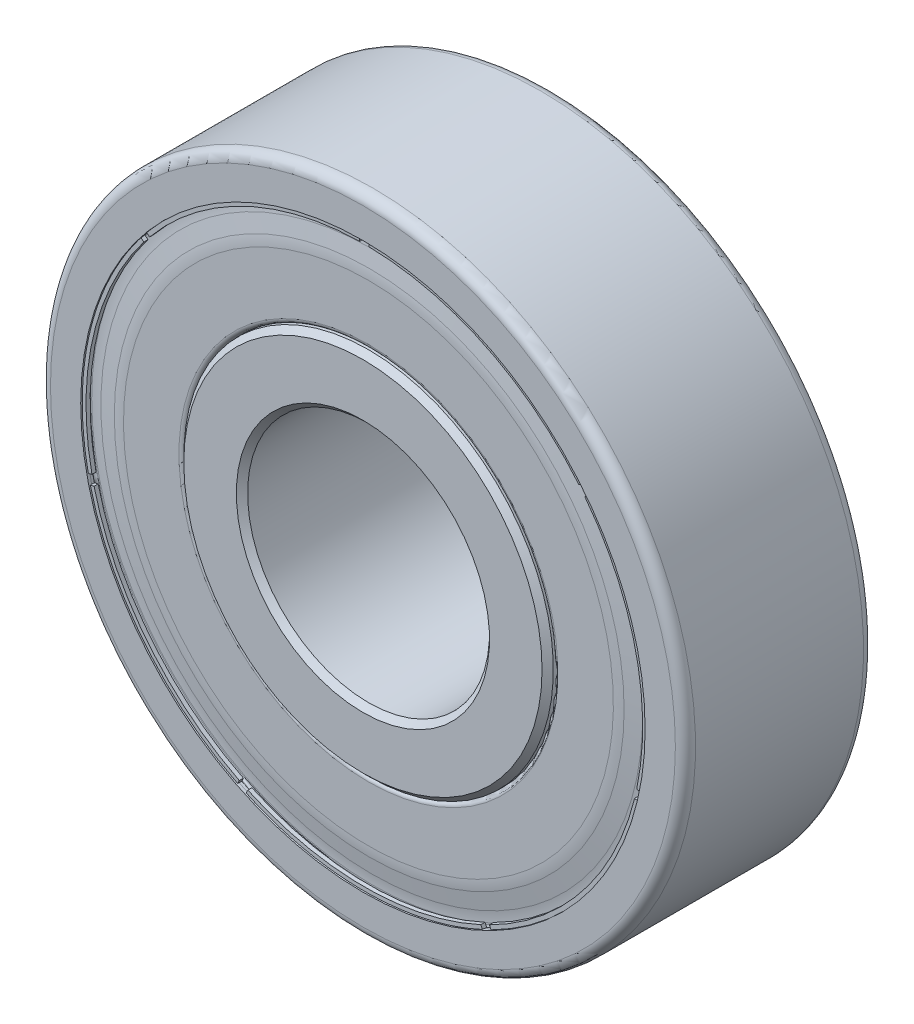
SolidWorks part; units mm, degrees
ref_plane "Front Plane" through (0, 0, 0) normal (0, 0, 1) x (1, 0, 0)
ref_plane "Top Plane" through (0, 0, 0) normal (0, 1, 0) x (1, 0, 0)
ref_plane "Right Plane" through (0, 0, 0) normal (1, 0, 0) x (0, 0, -1)
sketch "Sketch1" plane through (0, 0, 0) normal (0, 0, 1) x (1, 0, 0)
  line L0 (-12, 0) -> (-4.5, 0) construction
  line L1 (-4.5, 0) -> (4.5, 0) construction
  line L2 (4.5, 0) -> (12, 0) construction
  line L3 (0, 12) -> (0, 4.5) construction
  line L4 (0, 4.5) -> (0, 0) construction
  circle A0 centre (0, 0) radius 4.5 construction
  circle A1 centre (0, 0) radius 12 construction
  point P0 (0, 0)
  point P9 (0, 12)
  point P10 (0, 4.5)
  dimension "For Housing ID" = 24
  dimension "For Shaft Diameter" = 9
  dimension "OD" = 24
  dimension "ID" = 9
sketch "Sketch2" plane through (0, 0, 0) normal (1, 0, 0) x (0, 0, -1)
  line L1 (-3.5, -12) -> (3.5, -12) construction
  line L2 (-3.5, -12) -> (-3.5, 12) construction
  line L3 (-3.5, 12) -> (3.5, 12) construction
  line L4 (3.5, -12) -> (3.5, 12) construction
  line L5 (0, 12) -> (0, -12) construction
  line L6 (-3.5, 0) -> (3.5, 0) construction
  dimension "Width" = 7
sketch "Sketch3" plane through (0, 0, 0) normal (1, 0, 0) x (0, 0, -1)
  line L0 (-3.125, 12) -> (3.5, 12) construction
  line L1 (-3.5, 4.5) -> (3.5, 4.5)
  line L2 (-3.5, -12) -> (-3.5, 12) construction
  line L3 (3.5, -12) -> (3.5, 12) construction
  line L4 (-3.5, 4.5) -> (-3.5, 6.875)
  line L5 (-3.5, 6.875) -> (3.5, 6.875) construction
  line L6 (3.5, 6.875) -> (3.5, 4.5)
  line L7 (-3.5, 12) -> (-3.5, 10.5) construction
  line L8 (-3.5, 10.5) -> (3.5, 10.5) construction
  line L9 (3.5, 10.5) -> (3.5, 12) construction
  line L10 (0, 10.5) -> (0, 6.875) construction
  line L11 (0, 10.875) -> (0, 10.5) construction
  line L12 (0, 10.875) -> (0, 11.25) construction
  line L13 (0, 12) -> (0, 4.5) construction
  line L14 (0, 11.25) -> (0, 11.625) construction
  line L15 (0, 11.625) -> (0, 12) construction
  line L21 (3.5, 10.5) -> (3.395, 10.5)
  line L22 (-3.5, 10.5) -> (-3.395, 10.5)
  line L23 (-3.0477, 10.5304) -> (-2.9365, 9.9)
  line L24 (-2.9365, 9.9) -> (-1.8207, 9.9)
  line L25 (1.8207, 9.9) -> (2.9365, 9.9)
  line L26 (2.9365, 9.9) -> (3.0477, 10.5304)
  line L27 (-3.5, 6.875) -> (-1.2247, 6.875)
  line L28 (3.5, 6.875) -> (1.2247, 6.875)
  line L29 (-3.125, 12) -> (3.125, 12)
  line L31 (3.5, 11.625) -> (3.5, 10.5)
  line L33 (-3.5, 11.625) -> (-3.5, 10.5)
  circle A0 centre (0, 8.6875) radius 2.1875 construction
  arc A3 (-3.395, 10.5) -> (-3.0477, 10.5304) centre (-3.22, 10.5) cw
  arc A4 (3.0477, 10.5304) -> (3.395, 10.5) centre (3.22, 10.5) cw
  arc A5 (-1.8207, 9.9) -> (1.8207, 9.9) centre (0, 8.6875) cw
  arc A8 (-1.2247, 6.875) -> (1.2247, 6.875) centre (0, 8.6875) ccw
  arc A9 (-3.125, 12) -> (-3.5, 11.625) centre (-3.125, 11.625) ccw
  arc A10 (3.5, 11.625) -> (3.125, 12) centre (3.125, 11.625) ccw
  dimension "D1" = 4.375
  dimension "D5" = 0.175
  dimension "REF" = 7.5
  dimension "D2" = 1.5
  dimension "D3" = 0.105
  dimension "D4" = 10
  dimension "D6" = 0.6
revolve "Revolve1" add sketch "Sketch3" angle 360 about L6
sketch "Sketch7" plane through (0, 0, 0) normal (0, 0, 1) x (1, 0, 0)
  line L0 (0, 12) -> (0, 0) construction
  line L1 (0, 6.5) -> (0, 10.875) construction
  line L2 (-2.117, 8.1367) -> (0, 0) construction
  line L3 (0, 0) -> (2.117, 8.1367) construction
  circle A0 centre (0, 8.6875) radius 2.1875 construction
  point P8 (0, 6.5)
  dimension "Bearing Spacing" = 29.168
chamfer "Chamfer1" distance 0.21 angle 45 4 edges at (0, -4.5, -3.5) (0, -6.875, -3.5) (0, -4.5, 3.5) (0, -6.875, 3.5)
sketch "Sketch4" plane through (0, 0, 0) normal (1, 0, 0) x (0, 0, -1)
  line L0 (-3.395, 10.5) -> (-3.4475, 10.5)
  line L1 (-3.4475, 10.5) -> (-3.4475, 10.356)
  line L2 (-2.9365, 9.9) -> (-3.0477, 10.5304) construction
  line L3 (-3.4475, 10.5) -> (-3.5, 10.5) construction
  line L4 (-3.045, 10.5) -> (-3.045, 10.26)
  line L19 (-3.145, 10.26) -> (-3.045, 10.26) construction
  line L23 (-3.195, 9.3) -> (-3.195, 6.975) construction
  line L25 (-3.195, 6.975) -> (-2.1283, 6.975) construction
  line L26 (-2.1283, 6.975) -> (-2.1283, 6.875)
  line L28 (-2.1283, 6.875) -> (-3.295, 6.875) construction
  line L29 (-3.295, 6.875) -> (-3.295, 9.3) construction
  line L30 (-3.045, 10.26) -> (-3.195, 9.3)
  line L31 (-3.145, 10.26) -> (-3.145, 10.5)
  line L33 (-3.5, 6.875) -> (-1.2247, 6.875) construction
  line L35 (-3.4475, 10.356) -> (-3.295, 10.356)
  line L36 (-3.295, 10.356) -> (-3.295, 10.5)
  line L37 (-3.195, 8.1375) -> (-3.295, 8.1375) construction
  line L38 (-3.145, 10.26) -> (-3.295, 9.3)
  line L39 (-3.295, 10.356) -> (-3.295, 9.3) construction
  line L41 (-3.12, 6.875) -> (-2.1283, 6.875)
  line L42 (-3.12, 6.975) -> (-2.1283, 6.975)
  line L43 (-3.195, 7.05) -> (-3.195, 9.3)
  line L44 (-3.295, 9.3) -> (-3.295, 7.05)
  arc A0 (-3.045, 10.5) -> (-3.395, 10.5) centre (-3.22, 10.5) ccw
  arc A8 (-3.0477, 10.5304) -> (-3.395, 10.5) centre (-3.22, 10.5) ccw construction
  arc A9 (-3.145, 10.5) -> (-3.295, 10.5) centre (-3.22, 10.5) ccw
  arc A10 (-3.295, 7.05) -> (-3.12, 6.875) centre (-3.12, 7.05) ccw
  arc A11 (-3.195, 7.05) -> (-3.12, 6.975) centre (-3.12, 7.05) ccw
  point P24 (-3, 10.26)
  dimension "D4" = 0.35
  dimension "D1" = 0.144
  dimension "D2" = 0.1
  dimension "D5" = 1.1667
  dimension "D6" = 0.24
  dimension "D3" = 0.96
revolve "Revolve2" add sketch "Sketch4" angle 360 about L6
fillet "Fillet1" radius 2.4 2 edges at (0, -9.3, 3.295) (0, -10.26, 3.145)
sketch "Sketch5" plane through (0, 0, 0) normal (1, 0, 0) x (0, 0, -1)
  line L0 (0, 10.875) -> (0, 6.5)
  circle A0 centre (0, 8.6875) radius 2.1875 construction
  arc A1 (0, 6.5) -> (0, 10.875) centre (0, 8.6875) ccw
revolve "Revolve3" add sketch "Sketch5" angle 360 about L0
pattern_circular "CirPattern1" count 7 over 360 about axis through (0, 0, 0) along (0, 0, 1) of bodies 107
sketch "Sketch6" plane through (0, 0, 3.4475) normal (0, 0, 1) x (1, 0, 0)
  line L0 (0, 10.5) -> (0, 0) construction
  line L1 (-0.175, 10.4985) -> (-0.175, 10.3545)
  line L2 (0.175, 10.4985) -> (0.175, 10.3545)
  line L3 (-0.175, 10.4265) -> (0.175, 10.4265) construction
  arc A0 (0.175, 10.3545) -> (-0.175, 10.3545) centre (0, 0) ccw
  arc A1 (0.175, 10.4985) -> (-0.175, 10.4985) centre (0, 0) ccw
  circle A7 centre (0, 0) radius 10.5 construction
  circle A8 centre (0, 0) radius 10.356 construction
  circle A9 centre (0, 0) radius 10.5 construction
  circle A10 centre (0, 0) radius 10.356 construction
  point P13 (0, 10.4265)
  dimension "D1" = 0.35
extrude "Cut-Extrude1" cut sketch "Sketch6" against normal up to surface (0.1525 mm away) up to face at (0, -10.5, 3.295)
pattern_circular "CirPattern2" count 7 over 360 about axis through (0, 0, 0) along (0, 0, 1) of "Cut-Extrude1"
mirror "Mirror2" about plane through (0, 0, 0) normal (0, 0, 1) of bodies 127 106
equation "\"D1@Sketch3\"=\"Width@Sketch2\"*.625"
equation "\"D2@Sketch3\"=\"OD@Sketch1\" * .0625"
equation "\"D3@Sketch3\"=\"Width@Sketch2\"*.015"
equation "\"D5@Sketch3\"=\"Width@Sketch2\"*.025"
equation "\"D6@Sketch3\" = \"OD@Sketch1\" * .025"
equation "\"D1@Chamfer1\"=\"Width@Sketch2\"*.03"
equation "\"D1@Fillet1\"=\"OD@Sketch1\"*.1"
equation "\"D1@CirPattern1\"=(360/\"Bearing Spacing@Sketch7\")-5"
equation "\"D1@CirPattern2\" = ( 360 / \"Bearing Spacing@Sketch7\" ) - 5"
equation "\"D1@Sketch4\"=\"OD@Sketch1\" *.006"
equation "\"D5@Sketch4\"=\"Width@Sketch2\"/6"
equation "\"D6@Sketch4\"=\"OD@Sketch1\" * .01"
equation "\"D3@Sketch4\"=\"OD@Sketch1\" *.04"
equation "\"D1@Sketch6\"=\"Width@Sketch2\"*.05"
equation "\"D4@Sketch4\"=\"Width@Sketch2\"*.05"
